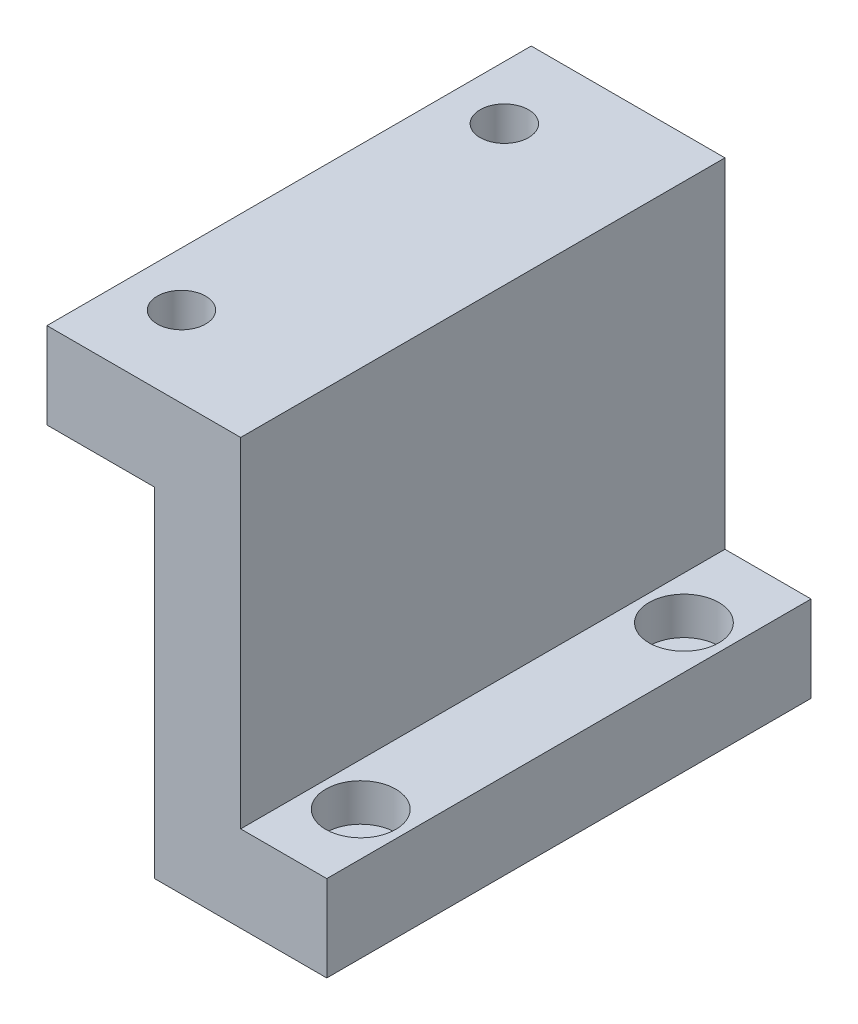
SolidWorks part; units mm, degrees
ref_plane "Front Plane" through (0, 0, 0) normal (0, 0, 1) x (1, 0, 0)
ref_plane "Top Plane" through (0, 0, 0) normal (0, 1, 0) x (1, 0, 0)
ref_plane "Right Plane" through (0, 0, 0) normal (1, 0, 0) x (0, 0, -1)
sketch "Sketch1" plane through (0, 0, 0) normal (0, 0, 1) x (1, 0, 0)
  line L1 (-4.5886, 8.5411) -> (13.4114, 8.5411)
  line L2 (-4.5886, 8.5411) -> (-4.5886, 0.5411)
  line L3 (-4.5886, 0.5411) -> (5.4114, 0.5411)
  line L6 (13.4114, 8.5411) -> (13.4114, -22.9589)
  line L8 (5.4114, 0.5411) -> (5.4114, -30.9589)
  line L9 (5.4114, -30.9589) -> (21.4114, -30.9589)
  line L11 (13.4114, -22.9589) -> (21.4114, -22.9589)
  line L12 (21.4114, -30.9589) -> (21.4114, -22.9589)
  point P5 (11.8481, 4.5762)
  point P11 (0, 0)
  point P12 (5.4114, -22.7563)
  dimension "D1" = 18
  dimension "D2" = 26
  dimension "D3" = 10
  dimension "D4" = 8
  dimension "D5" = 39.5
  dimension "D6" = 31.5
extrude "Boss-Extrude1" add sketch "Sketch1" along normal blind 45
sketch "Sketch2" plane through (0, 8.5411, 0) normal (0, 1, 0) x (1, 0, 0)
  line L1 (13.4114, -45) -> (-4.5886, -45) construction
  line L3 (-4.5886, -45) -> (-4.5886, 0) construction
  circle A0 centre (0.4114, -7.5) radius 2.25
  circle A1 centre (0.4114, -37.5) radius 2.25
  dimension "D1" = 4.5
  dimension "D2" = 7.5
  dimension "D3" = 37.5
  dimension "D4" = 5
  dimension "D5" = 5
extrude "Cut-Extrude1" cut sketch "Sketch2" against normal blind 45
sketch "Sketch3" plane through (0, -22.9589, 0) normal (0, 1, 0) x (1, 0, 0)
  line L0 (21.4114, -45) -> (21.4114, 0) construction
  circle A0 centre (17.4114, -7.8106) radius 1.7
  circle A1 centre (17.4114, -37.8432) radius 1.7
  point P4 (0, 0)
  dimension "D2" = 3.4
  dimension "D3" = 3.4
  dimension "D1" = 4
extrude "Cut-Extrude2" cut sketch "Sketch3" against normal blind 45
sketch "Sketch4" plane through (0, -22.9589, 0) normal (0, 1, 0) x (1, 0, 0)
  circle A0 centre (17.4114, -7.8106) radius 3.25
  circle A1 centre (17.4114, -37.8432) radius 3.25
  dimension "D1" = 6.5
extrude "Cut-Extrude3" cut sketch "Sketch4" against normal blind 3.5
